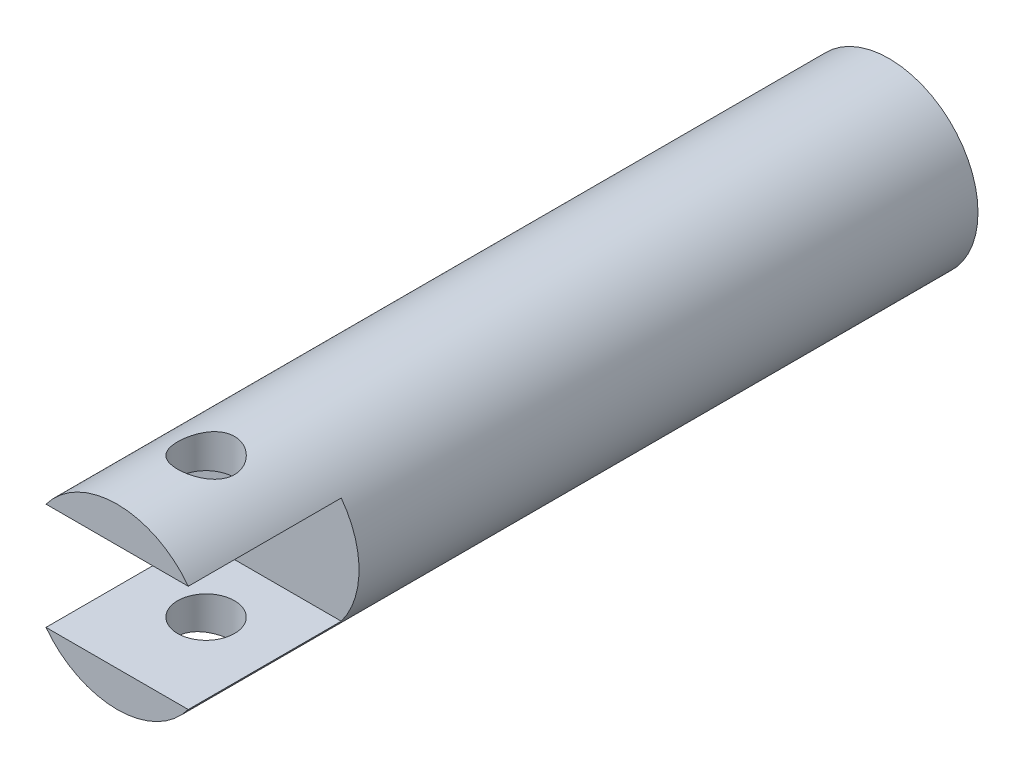
SolidWorks part; units mm, degrees
ref_plane "Front Plane" through (0, 0, 0) normal (0, 0, 1) x (1, 0, 0)
ref_plane "Top Plane" through (0, 0, 0) normal (0, 1, 0) x (1, 0, 0)
ref_plane "Right Plane" through (0, 0, 0) normal (1, 0, 0) x (0, 0, -1)
sketch "Sketch1" plane through (0, 0, 0) normal (0, 0, 1) x (1, 0, 0)
  circle A0 centre (0, 0) radius 25
  dimension "D1" = 50
extrude "Boss-Extrude1" add sketch "Sketch1" along normal blind 217
cosmetic thread "Cosmetic Thread1" parameters "D1"=35, "D2"=48
sketch "Sketch2" plane through (0, 0, 0) normal (0, 0, -1) x (-1, 0, 0)
  circle A0 centre (0, 0) radius 19
  dimension "D1" = 38
extrude "Cut-Extrude1" cut sketch "Sketch2" against normal blind 10
sketch "Sketch3" plane through (0, 0, 10) normal (0, 0, -1) x (-1, 0, 0)
  circle A0 centre (0, 0) radius 14
  dimension "D1" = 28
extrude "Cut-Extrude2" cut sketch "Sketch3" against normal blind 10
sketch "Sketch4" plane through (0, 0, 0) normal (1, 0, 0) x (0, 0, -1)
  line L0 (-217, 25) -> (-217, -25) construction
  line L1 (-217, 15) -> (-174, 15)
  line L2 (-217, 15) -> (-217, -15)
  line L3 (-217, -15) -> (-174, -15)
  line L4 (-174, 15) -> (-174, -15)
  dimension "D1" = 15
  dimension "D2" = 30
  dimension "D3" = 43
extrude "Cut-Extrude3" cut sketch "Sketch4" against normal through all both and the other way through all
sketch "Sketch5" plane through (0, 0, 0) normal (0, 1, 0) x (1, 0, 0)
  line L0 (-20, -217) -> (20, -217) construction
  circle A0 centre (0, -192) radius 8
  dimension "D1" = 16
  dimension "D2" = 25
extrude "Cut-Extrude4" cut sketch "Sketch5" against normal through all both and the other way through all
